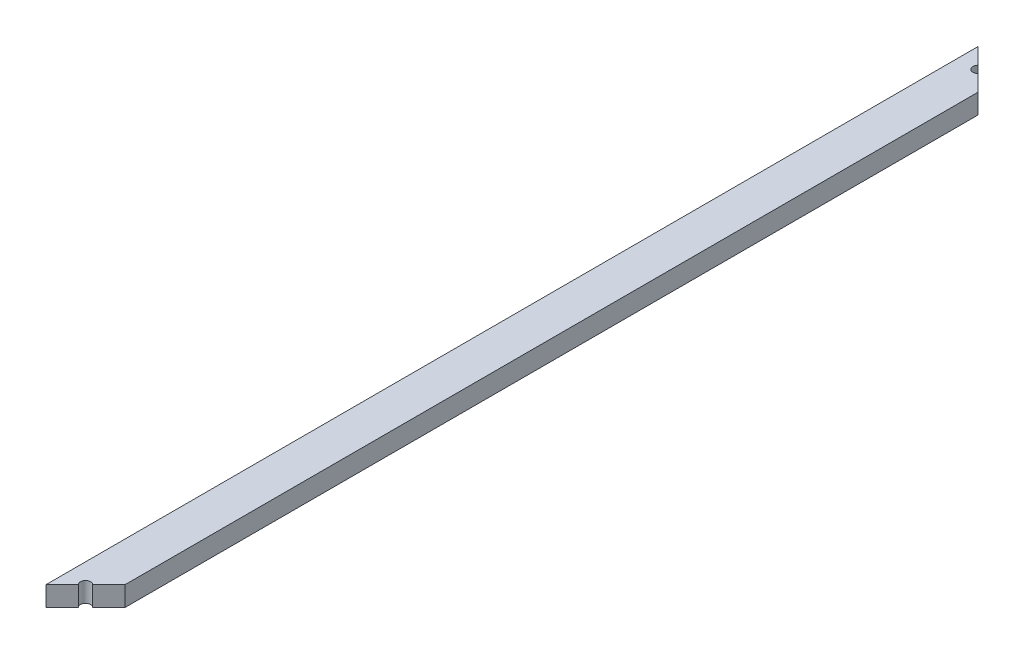
SolidWorks part; units mm, degrees
ref_plane "Front Plane" through (0, 0, 0) normal (0, 0, 1) x (1, 0, 0)
ref_plane "Top Plane" through (0, 0, 0) normal (0, 1, 0) x (1, 0, 0)
ref_plane "Right Plane" through (0, 0, 0) normal (1, 0, 0) x (0, 0, -1)
sketch "Sketch1" plane through (0, 0, 0) normal (0, 0, 1) x (1, 0, 0)
  line L1 (0, 0) -> (14, 0)
  line L2 (0, 0) -> (0, 7)
  line L3 (0, 7) -> (14, 7)
  line L4 (14, 0) -> (14, 7)
  dimension "D1" = 7
  dimension "D2" = 14
extrude "Boss-Extrude1" add sketch "Sketch1" along normal blind 330
sketch "Sketch2" plane through (0, 7, 0) normal (0, 1, 0) x (1, 0, 0)
  line L0 (0, 0) -> (14, -14)
  line L1 (14, -330) -> (14, 0) construction
  line L2 (14, -14) -> (14, 0)
  line L3 (14, 0) -> (0, 0)
  line L4 (14, -165) -> (0, -165) construction
  line L5 (0, -330) -> (0, 0) construction
  line L6 (14, -330) -> (0, -330)
  line L7 (14, -316) -> (14, -330)
  line L8 (0, -330) -> (14, -316)
  dimension "D1" = 45
extrude "Cut-Extrude1" cut sketch "Sketch2" against normal through all
sketch "Sketch3" plane through (0, 7, 0) normal (0, 1, 0) x (1, 0, 0)
  line L0 (0, 0) -> (14, -14) construction
  line L1 (0, -165) -> (14, -165) construction
  line L2 (0, -330) -> (0, 0) construction
  line L3 (14, -316) -> (14, -14) construction
  line L4 (5.7272, -5.7272) -> (8.2728, -8.2728)
  line L5 (5.7272, -324.2728) -> (8.2728, -321.7272)
  arc A0 (5.7272, -5.7272) -> (8.2728, -8.2728) centre (7, -7) ccw
  arc A1 (5.7272, -324.2728) -> (8.2728, -321.7272) centre (7, -323) cw
  dimension "D1" = 3.6
extrude "Cut-Extrude2" cut sketch "Sketch3" against normal through all
